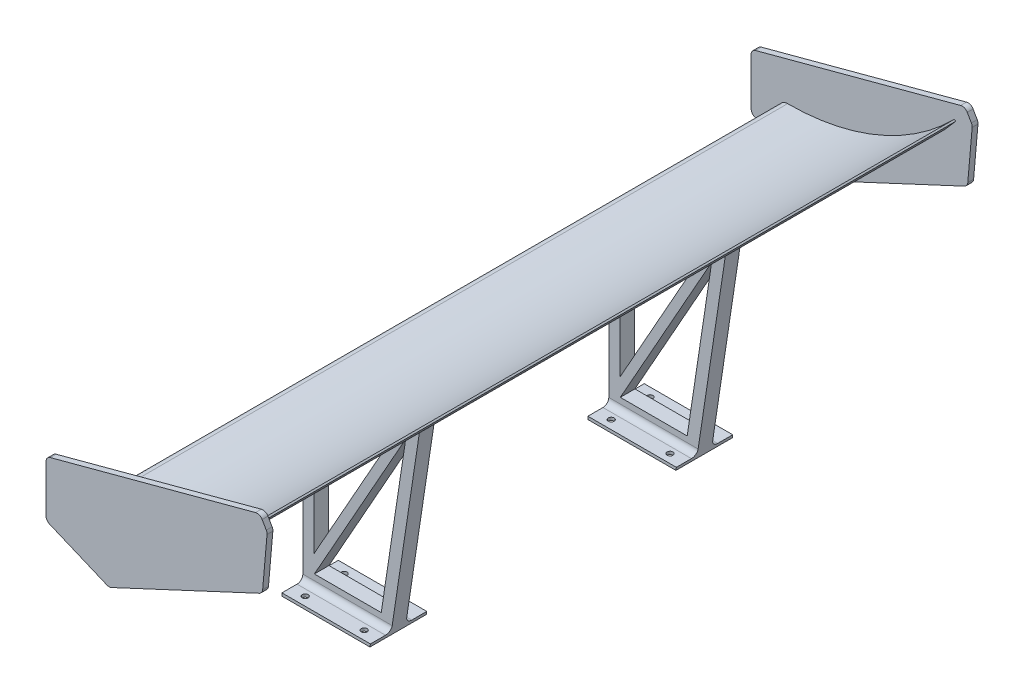
SolidWorks part; units mm, degrees
ref_plane "Front Plane" through (0, 0, 0) normal (0, 0, 1) x (1, 0, 0)
ref_plane "Top Plane" through (0, 0, 0) normal (0, 1, 0) x (1, 0, 0)
ref_plane "Right Plane" through (0, 0, 0) normal (1, 0, 0) x (0, 0, -1)
sketch "Sketch1" plane through (0, 0, 0) normal (0, 0, 1) x (1, 0, 0)
  line L0 (0, 75) -> (300, 75) construction
  line L1 (300, 150) -> (0, 150) construction
  line L2 (0, 150) -> (0, 0) construction
  line L3 (0, 0) -> (300, 0) construction
  line L4 (300, 0) -> (300, 150) construction
  line L5 (15, 14.9738) -> (302.2901, 148.9393) construction
  line L6 (301.2294, 150) -> (303.3507, 147.8787)
  arc A0 (15.8866, 0) -> (15, 29.9738) centre (15, 14.9738) cw
  arc A1 (15.8866, 0) -> (303.3507, 147.8787) centre (-7.7553, 399.3007) ccw
  arc A2 (15, 29.9738) -> (301.2294, 150) centre (15.5462, 429.9734) ccw
  dimension "D4" = 15
  dimension "D3" = 400
  dimension "D5" = 400
  dimension "D1" = 150
  dimension "D2" = 300
  dimension "D6" = 45
  dimension "D7" = 3
  dimension "D8" = 25
extrude "Boss-Extrude1" add sketch "Sketch1" along normal mid plane 1200 contours A2 L6 A1 A0
sketch "Sketch2" plane through (0, 0, 600) normal (0, 0, 1) x (1, 0, 0)
  line L0 (-47.6016, 79.4522) -> (-47.6016, -15.5478)
  line L1 (-47.6016, -15.5478) -> (60.8411, -61.045)
  line L2 (60.8411, -61.045) -> (323.6704, 61.5143)
  line L3 (323.6704, 61.5143) -> (331.9502, 156.1528)
  line L5 (331.9502, 156.1528) -> (319.4502, 177.8034)
  line L6 (319.4502, 177.8034) -> (-47.6016, 79.4522)
  dimension "D2" = 95
  dimension "D3" = 105
  dimension "D4" = 255
  dimension "D5" = 215
  dimension "D6" = 120
  dimension "D7" = 290
  dimension "D8" = 95
  dimension "D9" = 380
  dimension "D10" = 25
extrude "Boss-Extrude2" add sketch "Sketch2" along normal blind 10
fillet "Fillet1" radius 10 6 edges at (319.4502, 177.8034, 605) (331.9502, 156.1528, 605) (323.6704, 61.5143, 605) (60.8411, -61.045, 605) (-47.6016, -15.5478, 605) (-47.6016, 79.4522, 605)
mirror "Mirror2" about plane through (0, 0, 0) normal (0, 0, 1) of "Fillet1", "Boss-Extrude2"
sketch "Sketch3" plane through (0, 0, 0) normal (0, 1, 0) x (1, 0, 0)
  line L0 (0, 0) -> (303.3507, 0) construction
  line L2 (58.1147, -250) -> (258.1147, -250)
  line L3 (158.1147, 600) -> (158.1147, -600) construction
  line L4 (15, 600) -> (301.2294, 600) construction
  line L5 (301.2294, -600) -> (15, -600) construction
  line L6 (0, 600) -> (0, -600) construction
  line L7 (303.3507, -600) -> (303.3507, 600) construction
  line L8 (58.1147, -250) -> (58.1147, -275)
  line L9 (58.1147, -275) -> (258.1147, -275)
  line L10 (258.1147, -250) -> (258.1147, -275)
  line L11 (58.1147, -250) -> (258.1147, -275) construction
  line L12 (58.1147, -275) -> (258.1147, -250) construction
  point P19 (158.1147, -262.5)
  dimension "D1" = 200
  dimension "D2" = 25
  dimension "D3" = 250
extrude "Boss-Extrude3" add sketch "Sketch3" along normal up to next and the other way blind 220
mirror "Mirror3" about plane through (0, 0, 0) normal (0, 0, 1) of "Boss-Extrude3"
sketch "Sketch4" plane through (0, -220, 0) normal (0, -1, 0) x (1, 0, 0)
  line L0 (58.1147, 262.5) -> (258.1147, 262.5) construction
  line L1 (58.1147, 250) -> (58.1147, 275) construction
  line L2 (258.1147, 275) -> (258.1147, 250) construction
  line L4 (58.1147, 310.8693) -> (258.1147, 310.8693)
  line L5 (58.1147, 310.8693) -> (58.1147, 214.1307)
  line L6 (58.1147, 214.1307) -> (258.1147, 214.1307)
  line L7 (258.1147, 310.8693) -> (258.1147, 214.1307)
  line L8 (58.1147, 310.8693) -> (258.1147, 214.1307) construction
  line L9 (58.1147, 214.1307) -> (258.1147, 310.8693) construction
  point P6 (158.1147, 262.5)
extrude "Boss-Extrude4" add sketch "Sketch4" along normal blind 5
mirror "Mirror6" about plane through (0, 0, 0) normal (0, 0, 1) of "Boss-Extrude4"
fillet "Fillet3" radius 10 4 edges at (158.1147, -220, 275) (158.1147, -220, 250) (158.1147, -220, -275) (158.1147, -220, -250)
sketch "Sketch5" plane through (0, -225, 0) normal (0, -1, 0) x (1, 0, 0)
  line L0 (58.1147, 310.8693) -> (58.1147, 214.1307) construction
  line L1 (258.1147, 214.1307) -> (258.1147, 310.8693) construction
  line L2 (258.1147, 310.8693) -> (58.1147, 310.8693) construction
  line L3 (58.1147, 214.1307) -> (258.1147, 214.1307) construction
  circle A0 centre (83.1147, 295.8693) radius 5
  circle A1 centre (184.2147, 295.8693) radius 5
  circle A2 centre (184.2147, 229.1307) radius 5
  circle A3 centre (83.1147, 229.1307) radius 5
  point P8 (0, 0)
  point P9 (0, 0)
  point P10 (0, 0)
  point P11 (0, 0)
  point P12 (0, 0)
  point P13 (0, 0)
  dimension "D5" = 10
  dimension "D1" = 25
  dimension "D2" = 73.9
  dimension "D3" = 15
  dimension "D4" = 15
  dimension "D6" = 101.1
  dimension "D7" = 66.7386
extrude "Cut-Extrude1" cut sketch "Sketch5" against normal blind 5
mirror "Mirror7" about plane through (0, 0, 0) normal (0, 0, 1) of "Cut-Extrude1"
sketch "Sketch8" plane through (0, 0, 0) normal (0, 0, 1) x (1, 0, 0)
  line L0 (258.1147, 100) -> (209.2106, -225)
  line L1 (258.1147, -210) -> (258.1147, 100.4477) construction
  line L2 (258.1147, -225) -> (58.1147, -225) construction
  line L3 (209.2106, -225) -> (258.1147, -225)
  line L4 (258.1147, -225) -> (258.1147, 100)
  line L5 (192.6725, -200) -> (234.6267, 78.8132)
  line L6 (234.6267, 78.8132) -> (77.9081, -200)
  line L7 (77.9081, -200) -> (192.6725, -200)
  line L8 (77.407, -169.9189) -> (203.6979, 54.7615)
  line L9 (203.6979, 54.7615) -> (77.407, -7.8828)
  line L10 (77.407, -7.8828) -> (77.407, -169.9189)
  point P10 (203.6979, 54.7615)
  point P11 (77.407, -7.8828)
  dimension "D1" = 25
  dimension "D2" = 325
extrude "Cut-Extrude3" cut sketch "Sketch8" against normal up to next and the other way up to next
